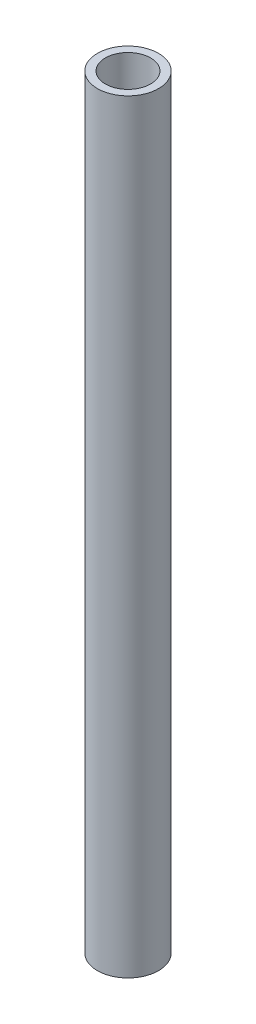
SolidWorks part; units mm, degrees
ref_plane "Front Plane" through (0, 0, 0) normal (0, 0, 1) x (1, 0, 0)
ref_plane "Top Plane" through (0, 0, 0) normal (0, 1, 0) x (1, 0, 0)
ref_plane "Right Plane" through (0, 0, 0) normal (1, 0, 0) x (0, 0, -1)
sketch "Sketch1" plane through (0, 0, 0) normal (0, 1, 0) x (1, 0, 0)
  circle A0 centre (0, 0) radius 7.8994
  circle A1 centre (0, 0) radius 10.668
  dimension "D1" = 15.7988
  dimension "D2" = 21.336
extrude "Boss-Extrude1" add sketch "Sketch1" along normal blind 266.7
